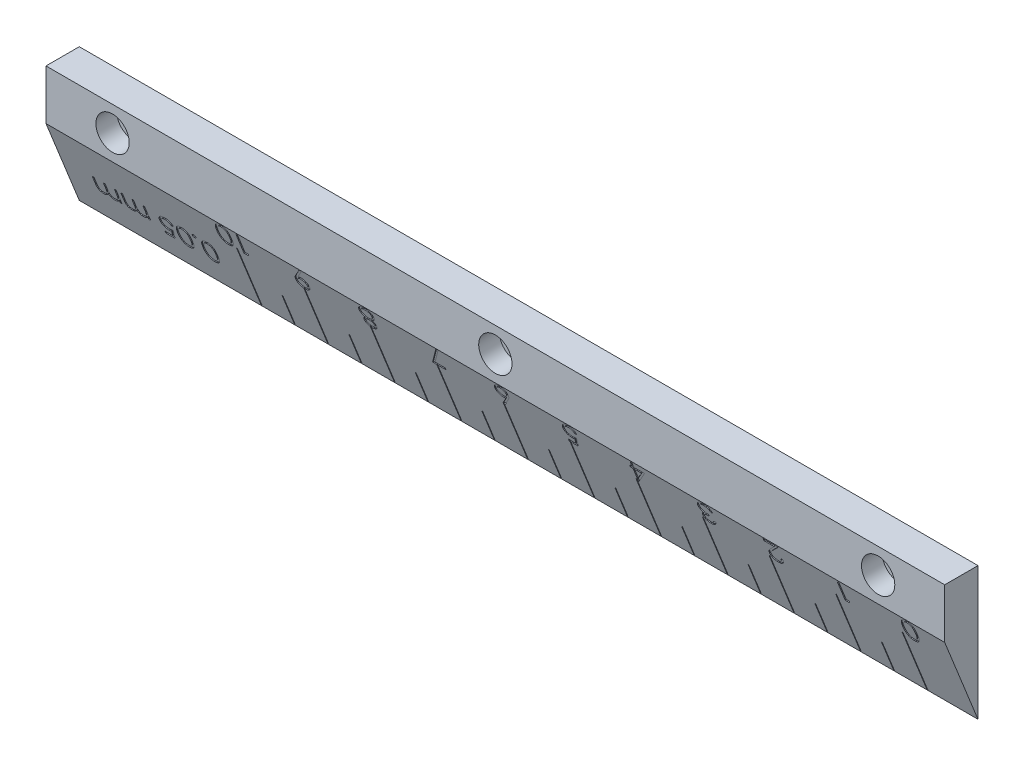
SolidWorks part; units mm, degrees
material "1.4000 (X6Cr13)"
ref_plane "Front Plane" through (0, 0, 0) normal (0, 0, 1) x (1, 0, 0)
ref_plane "Top Plane" through (0, 0, 0) normal (0, 1, 0) x (1, 0, 0)
ref_plane "Right Plane" through (0, 0, 0) normal (1, 0, 0) x (0, 0, -1)
sketch "Sketch1" plane through (0, 0, 0) normal (0, 0, 1) x (1, 0, 0)
  line L1 (-27, -4) -> (27, -4)
  line L2 (-27, -4) -> (-27, 4)
  line L3 (-27, 4) -> (27, 4)
  line L4 (27, -4) -> (27, 4)
  line L5 (-27, -4) -> (27, 4) construction
  line L6 (-27, 4) -> (27, -4) construction
  point P0 (0, 0)
  dimension "D1" = 8
  dimension "D2" = 54
extrude "Boss-Extrude1" add sketch "Sketch1" along normal blind 2
sketch "Sketch2" plane through (27, 0, 0) normal (1, 0, 0) x (0, 0, -1)
  line L0 (-2, 1) -> (0, -4)
  line L1 (-2, -4) -> (-2, 4) construction
  line L2 (0, -4) -> (-2, -4)
  line L3 (-2, -4) -> (-2, 1)
  line L4 (-2, 4) -> (0, 4) construction
  dimension "D1" = 3
extrude "Cut-Extrude1" cut sketch "Sketch2" against normal through all
sketch "Sketch3" plane through (0, 0, 2) normal (0, 0, 1) x (1, 0, 0)
  line L0 (-23, 2.5) -> (23, 2.5) construction
  line L1 (27, 4) -> (-27, 4) construction
  line L2 (27, 1) -> (27, 4) construction
  circle A0 centre (23, 2.5) radius 1
  circle A1 centre (0, 2.5) radius 1
  circle A2 centre (-23, 2.5) radius 1
  point P3 (0, 2.5)
  dimension "D2" = 2
  dimension "D3" = 4
  dimension "D1" = 1.5
extrude "Cut-Extrude2" cut sketch "Sketch3" against normal blind 1.25
sketch "Sketch4" plane through (0, 0, 0.75) normal (0, 0, 1) x (1, 0, 0)
  circle A0 centre (-23, 2.5) radius 0.5
  circle A1 centre (0, 2.5) radius 0.5
  circle A2 centre (23, 2.5) radius 0.5
  dimension "D1" = 1
extrude "Cut-Extrude3" cut sketch "Sketch4" against normal through all
sketch "Sketch5" plane through (0, -0.5517, 1.3793) normal (0, -0.3714, 0.9285) x (1, 0, 0)
  line L0 (27, -3.7139) -> (27, 1.6713) construction
  line L1 (23.95, 0.3361) -> (24, 0.3361)
  line L2 (23.95, 0.3361) -> (23.95, -3.6639)
  line L3 (23.95, -3.6639) -> (24, -3.6639)
  line L4 (24, 0.3361) -> (24, -3.6639)
  line L5 (-27, -3.7139) -> (27, -3.7139) construction
  line L6 (19.95, 0.3361) -> (20, 0.3361)
  line L7 (19.95, 0.3361) -> (19.95, -3.6639)
  line L8 (19.95, -3.6639) -> (20, -3.6639)
  line L9 (20, 0.3361) -> (20, -3.6639)
  line L10 (15.95, 0.3361) -> (16, 0.3361)
  line L11 (15.95, 0.3361) -> (15.95, -3.6639)
  line L12 (15.95, -3.6639) -> (16, -3.6639)
  line L13 (16, 0.3361) -> (16, -3.6639)
  line L14 (11.95, 0.3361) -> (12, 0.3361)
  line L15 (11.95, 0.3361) -> (11.95, -3.6639)
  line L16 (11.95, -3.6639) -> (12, -3.6639)
  line L17 (12, 0.3361) -> (12, -3.6639)
  line L18 (7.95, 0.3361) -> (8, 0.3361)
  line L19 (7.95, 0.3361) -> (7.95, -3.6639)
  line L20 (7.95, -3.6639) -> (8, -3.6639)
  line L21 (8, 0.3361) -> (8, -3.6639)
  line L22 (3.95, 0.3361) -> (4, 0.3361)
  line L23 (3.95, 0.3361) -> (3.95, -3.6639)
  line L24 (3.95, -3.6639) -> (4, -3.6639)
  line L25 (4, 0.3361) -> (4, -3.6639)
  line L26 (-0.05, 0.3361) -> (0, 0.3361)
  line L27 (-0.05, 0.3361) -> (-0.05, -3.6639)
  line L28 (-0.05, -3.6639) -> (0, -3.6639)
  line L29 (0, 0.3361) -> (0, -3.6639)
  line L30 (-4.05, 0.3361) -> (-4, 0.3361)
  line L31 (-4.05, 0.3361) -> (-4.05, -3.6639)
  line L32 (-4.05, -3.6639) -> (-4, -3.6639)
  line L33 (-4, 0.3361) -> (-4, -3.6639)
  line L34 (-8.05, 0.3361) -> (-8, 0.3361)
  line L35 (-8.05, 0.3361) -> (-8.05, -3.6639)
  line L36 (-8.05, -3.6639) -> (-8, -3.6639)
  line L37 (-8, 0.3361) -> (-8, -3.6639)
  line L38 (-12.05, 0.3361) -> (-12, 0.3361)
  line L39 (-12.05, 0.3361) -> (-12.05, -3.6639)
  line L40 (-12.05, -3.6639) -> (-12, -3.6639)
  line L41 (-12, 0.3361) -> (-12, -3.6639)
  line L42 (-16.05, 0.3361) -> (-16, 0.3361)
  line L43 (-16.05, 0.3361) -> (-16.05, -3.6639)
  line L44 (-16.05, -3.6639) -> (-16, -3.6639)
  line L45 (-16, 0.3361) -> (-16, -3.6639)
  line L46 (17.95, -1.6639) -> (18, -1.6639)
  line L47 (21.95, -1.6639) -> (22, -1.6639)
  line L48 (21.95, -1.6639) -> (21.95, -3.6639)
  line L49 (21.95, -3.6639) -> (22, -3.6639)
  line L50 (22, -1.6639) -> (22, -3.6639)
  line L51 (17.95, -1.6639) -> (17.95, -3.6639)
  line L52 (17.95, -3.6639) -> (18, -3.6639)
  line L53 (18, -1.6639) -> (18, -3.6639)
  line L54 (13.95, -1.6639) -> (14, -1.6639)
  line L55 (13.95, -1.6639) -> (13.95, -3.6639)
  line L56 (13.95, -3.6639) -> (14, -3.6639)
  line L57 (14, -1.6639) -> (14, -3.6639)
  line L58 (9.95, -1.6639) -> (10, -1.6639)
  line L59 (9.95, -1.6639) -> (9.95, -3.6639)
  line L60 (9.95, -3.6639) -> (10, -3.6639)
  line L61 (10, -1.6639) -> (10, -3.6639)
  line L62 (5.95, -1.6639) -> (6, -1.6639)
  line L63 (5.95, -1.6639) -> (5.95, -3.6639)
  line L64 (5.95, -3.6639) -> (6, -3.6639)
  line L65 (6, -1.6639) -> (6, -3.6639)
  line L66 (1.95, -1.6639) -> (2, -1.6639)
  line L67 (1.95, -1.6639) -> (1.95, -3.6639)
  line L68 (1.95, -3.6639) -> (2, -3.6639)
  line L69 (2, -1.6639) -> (2, -3.6639)
  line L70 (-2.05, -1.6639) -> (-2, -1.6639)
  line L71 (-2.05, -1.6639) -> (-2.05, -3.6639)
  line L72 (-2.05, -3.6639) -> (-2, -3.6639)
  line L73 (-2, -1.6639) -> (-2, -3.6639)
  line L74 (-6.05, -1.6639) -> (-6, -1.6639)
  line L75 (-6.05, -1.6639) -> (-6.05, -3.6639)
  line L76 (-6.05, -3.6639) -> (-6, -3.6639)
  line L77 (-6, -1.6639) -> (-6, -3.6639)
  line L78 (-10.05, -1.6639) -> (-10, -1.6639)
  line L79 (-10.05, -1.6639) -> (-10.05, -3.6639)
  line L80 (-10.05, -3.6639) -> (-10, -3.6639)
  line L81 (-10, -1.6639) -> (-10, -3.6639)
  line L82 (-14.05, -1.6639) -> (-14, -1.6639)
  line L83 (-14.05, -1.6639) -> (-14.05, -3.6639)
  line L84 (-14.05, -3.6639) -> (-14, -3.6639)
  line L85 (-14, -1.6639) -> (-14, -3.6639)
  dimension "D1" = 3
  dimension "D2" = 0.05
  dimension "D3" = 0.05
  dimension "D4" = 4
  dimension "D6" = 4
  dimension "D7" = 2
  dimension "D8" = 2
  dimension "D9" = 0.05
  dimension "D10" = 0.05
  dimension "D12" = 4
  dimension "D5" = 11
  dimension "D11" = 10
extrude "Cut-Extrude4" cut sketch "Sketch5" against normal blind 0.05
sketch "Sketch6" plane through (0, -0.5517, 1.3793) normal (0, -0.3714, 0.9285) x (1, 0, 0)
  line L0 (-17.0856, 1.5705) -> (25.1802, 1.5705) construction
  text T0 "0      1      2      3      4      5      6      7      8      9     10" font "Century Gothic" height in points 5
extrude "Cut-Extrude5" cut sketch "Sketch6" against normal blind 0.05
sketch "Sketch7" plane through (0, -0.5517, 1.3793) normal (0, -0.3714, 0.9285) x (1, 0, 0)
  line L0 (-16, -0.765) -> (-27, -0.765) construction
  line L1 (-16, -3.5889) -> (-16, 0.3361) construction
  line L2 (-27, -3.7139) -> (-27, 1.6713) construction
  text T0 "0.05 mm" font "Century Gothic" height in points 5
extrude "Cut-Extrude6" cut sketch "Sketch7" against normal blind 0.05
